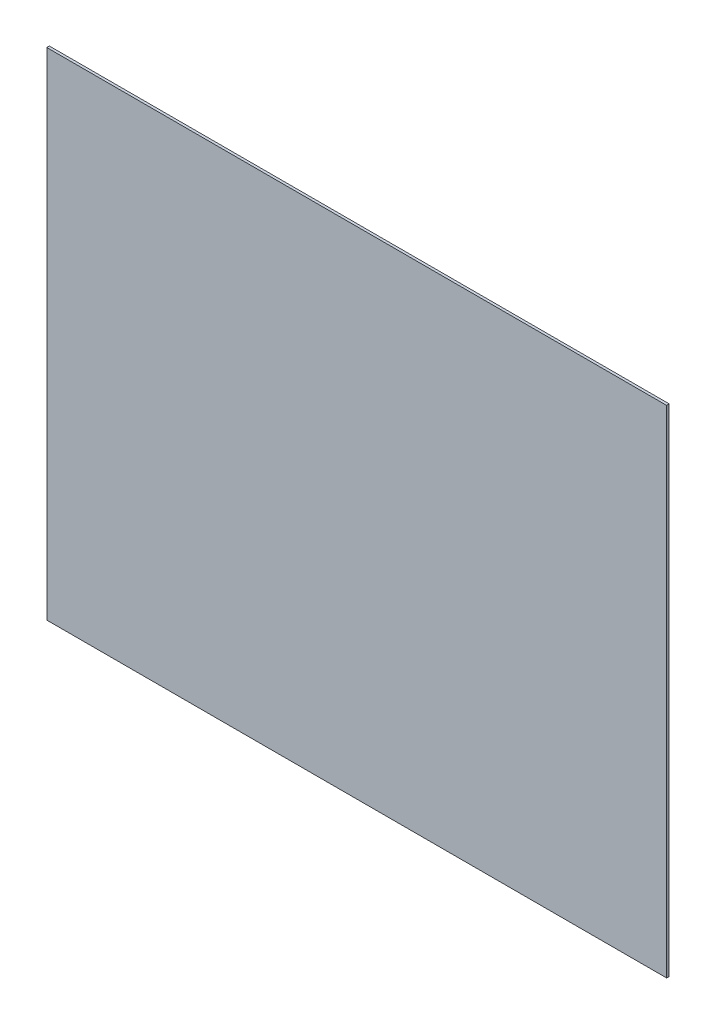
SolidWorks part; units mm, degrees
ref_plane "Front Plane" through (0, 0, 0) normal (0, 0, 1) x (1, 0, 0)
ref_plane "Top Plane" through (0, 0, 0) normal (0, 1, 0) x (1, 0, 0)
ref_plane "Right Plane" through (0, 0, 0) normal (1, 0, 0) x (0, 0, -1)
sketch "Sketch1" plane through (0, 0, 0) normal (0, 0, 1) x (1, 0, 0)
  line L1 (0, 0) -> (762, 0)
  line L2 (0, 0) -> (0, 609.6)
  line L3 (0, 609.6) -> (762, 609.6)
  line L4 (762, 0) -> (762, 609.6)
  dimension "D1" = 762
  dimension "D2" = 609.6
extrude "Extrude1" add sketch "Sketch1" along normal blind 3.175
